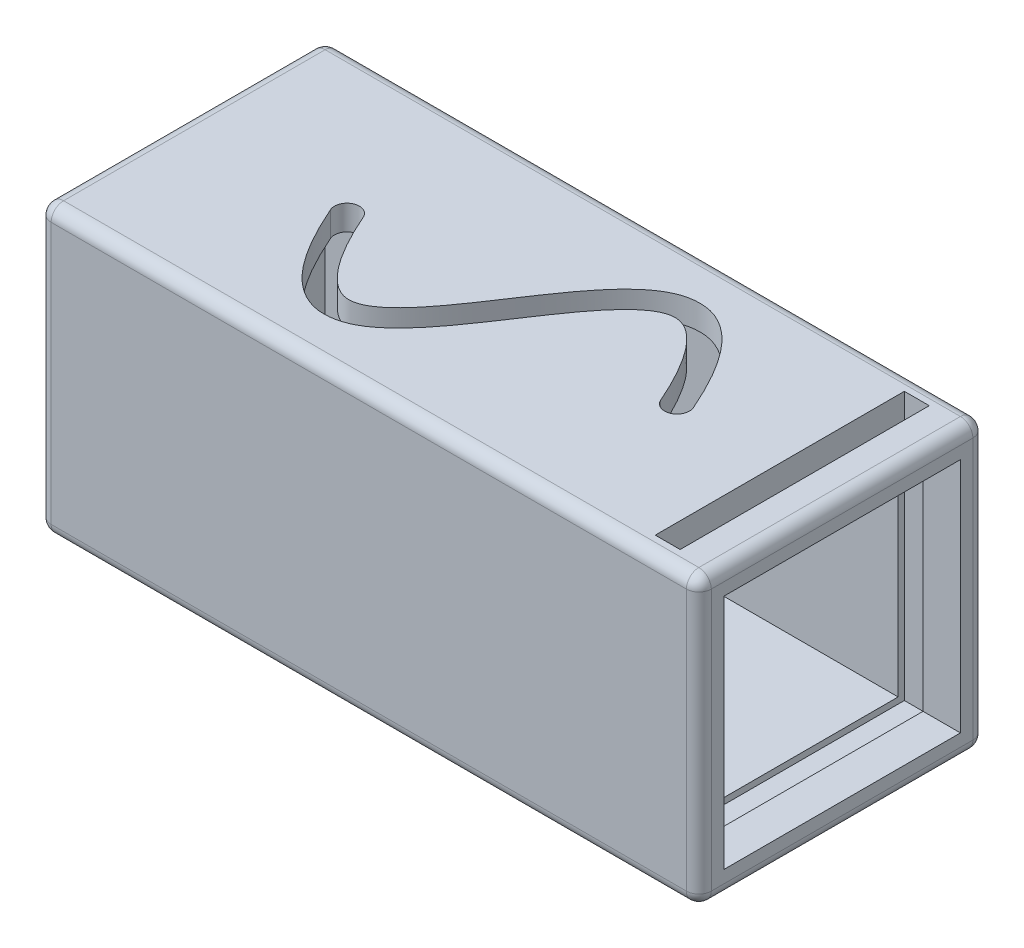
SolidWorks part; units mm, degrees
ref_plane "Front Plane" through (0, 0, 0) normal (0, 0, 1) x (1, 0, 0)
ref_plane "Top Plane" through (0, 0, 0) normal (0, 1, 0) x (1, 0, 0)
ref_plane "Right Plane" through (0, 0, 0) normal (1, 0, 0) x (0, 0, -1)
sketch "Sketch1" plane through (0, 0, 0) normal (0, 1, 0) x (1, 0, 0)
  line L0 (0, 11.5) -> (53, 11.5) construction
  line L1 (0, 0) -> (53, 0)
  line L2 (0, 0) -> (0, 23)
  line L3 (0, 23) -> (53, 23)
  line L4 (53, 0) -> (53, 23)
  line L5 (26.5, 23) -> (26.5, 0) construction
  line L6 (26.5, 23) -> (0, 0) construction
  line L7 (26.5, 23) -> (53, 0) construction
  line L8 (53, 23) -> (26.5, 0) construction
  line L9 (13.25, 11.5) -> (13.25, 23) construction
  line L10 (13.25, 11.5) -> (13.25, 0) construction
  line L11 (13.25, 23) -> (26.5, 11.5) construction
  line L12 (39.75, 11.5) -> (39.75, 0) construction
  line L13 (39.75, 0) -> (26.5, 11.5) construction
  arc A0 (14.168, 11.1034) -> (12.332, 11.8966) centre (13.25, 11.5) cw
  arc A1 (40.668, 11.1034) -> (38.832, 11.8966) centre (39.75, 11.5) ccw
  spline S0 degree 3 poles (13.25, 11.5) (17.6667, 21.7222) (26.5, 11.5) (35.3333, 1.2778) (39.75, 11.5) knots 0 0 0 0 0.5 1 1 1 1 construction
  spline S1 degree 1 poles (14.168, 11.1034) (40.668, 11.1034) knots 0 0 1 1 construction
  spline S2 degree 3 poles (14.168, 11.1034) (14.2958, 11.3992) (14.5701, 12.0052) (15.0936, 13.0483) (15.7438, 14.1469) (16.4921, 15.1239) (17.1955, 15.7936) (17.8364, 16.1939) (18.608, 16.4471) (19.553, 16.3923) (20.9516, 15.7092) (22.4917, 14.4327) (24.0966, 12.7515) (26.2868, 10.2186) (28.5265, 7.6182) (30.8893, 5.6467) (32.8016, 4.6526) (34.9868, 4.4793) (36.7555, 5.3352) (38.0231, 6.5593) (38.9304, 7.7509) (39.6641, 8.9943) (40.2372, 10.1372) (40.5305, 10.7852) (40.668, 11.1034) knots 0 0 0 0 0.015625 0.03125 0.0625 0.09375 0.125 0.15625 0.1875 0.25 0.3125 0.375 0.4375 0.5 0.625 0.6875 0.75 0.8125 0.875 0.90625 0.9375 0.96875 0.984375 1 1 1 1
  spline S3 degree 1 poles (12.332, 11.8966) (38.832, 11.8966) knots 0 0 1 1 construction
  spline S4 degree 3 poles (12.332, 11.8966) (12.4695, 12.2148) (12.7628, 12.8628) (13.3359, 14.0057) (14.0696, 15.2491) (14.9769, 16.4407) (16.2445, 17.6648) (18.0132, 18.5207) (20.1984, 18.3474) (22.1107, 17.3533) (24.4735, 15.3818) (26.7132, 12.7814) (28.9034, 10.2485) (30.5083, 8.5673) (32.0484, 7.2908) (33.447, 6.6077) (34.392, 6.5529) (35.1636, 6.8061) (35.8045, 7.2064) (36.5079, 7.8761) (37.2562, 8.8531) (37.9064, 9.9517) (38.4299, 10.9948) (38.7042, 11.6008) (38.832, 11.8966) knots 0 0 0 0 0.015625 0.03125 0.0625 0.09375 0.125 0.1875 0.25 0.3125 0.375 0.5 0.5625 0.625 0.6875 0.75 0.8125 0.84375 0.875 0.90625 0.9375 0.96875 0.984375 1 1 1 1
  dimension "D1" = 53
  dimension "D2" = 23
  dimension "D3" = 1
  dimension "D4" = 1
extrude "Boss-Extrude1" add sketch "Sketch1" along normal blind 2
sketch "Sketch3" plane through (0, 2, 0) normal (0, 1, 0) x (1, 0, 0)
  line L0 (2, 21) -> (51, 21)
  line L1 (0, 23) -> (53, 23)
  line L2 (0, 23) -> (0, 0)
  line L3 (0, 0) -> (53, 0)
  line L4 (53, 23) -> (53, 0)
  line L5 (51, 21) -> (51, 2)
  line L6 (2, 2) -> (51, 2)
  line L7 (2, 21) -> (2, 2)
  dimension "D1" = 2
extrude "Boss-Extrude2" add sketch "Sketch3" along normal blind 19
sketch "Sketch5" plane through (0, 21, 0) normal (0, 1, 0) x (1, 0, 0)
  line L1 (0, 23) -> (53, 23)
  line L2 (0, 23) -> (0, 0)
  line L3 (0, 0) -> (53, 0)
  line L4 (53, 23) -> (53, 0)
extrude "Boss-Extrude3" add sketch "Sketch5" along normal blind 2
sketch "Sketch7" plane through (0, 23, 0) normal (0, 1, 0) x (1, 0, 0)
  line L0 (0, 23) -> (26.5, 0) construction
  line L1 (0, 0) -> (53, 0) construction
  line L2 (26.5, 0) -> (53, 23) construction
  line L3 (53, 0) -> (53, 23) construction
  line L4 (53, 23) -> (0, 23) construction
  line L5 (26.5, 0) -> (26.5, 23) construction
  line L6 (13.25, 11.5) -> (39.75, 11.5) construction
  line L7 (26.5, 11.5) -> (20.8072, 4.9409) construction
  line L8 (39.75, 11.5) -> (26.5, 23) construction
  line L9 (26.5, 11.5) -> (32.1928, 18.0591) construction
  arc A0 (12.3342, 11.0983) -> (14.1658, 11.9017) centre (13.25, 11.5) cw
  arc A1 (38.8342, 11.0983) -> (40.6658, 11.9017) centre (39.75, 11.5) ccw
  spline S0 degree 3 poles (13.25, 11.5) (18.5153, -0.5021) (26.5, 11.5) (34.4847, 23.5021) (39.75, 11.5) knots 0 0 0 0 0.5 1 1 1 1 construction
  spline S1 degree 1 poles (12.3342, 11.0983) (38.8342, 11.0983) knots 0 0 1 1 construction
  spline S2 degree 3 poles (12.3342, 11.0983) (12.4963, 10.7288) (12.8406, 9.9742) (13.5006, 8.6486) (14.3249, 7.2107) (15.3106, 5.8408) (16.6448, 4.4414) (18.461, 3.4327) (20.7523, 3.6385) (22.6162, 4.8398) (24.8193, 7.1581) (26.8407, 10.2086) (28.8216, 13.1837) (30.2872, 15.1587) (31.7198, 16.6524) (32.8046, 17.2998) (33.5369, 17.4501) (34.0618, 17.4122) (34.6511, 17.1934) (35.3458, 16.7102) (36.1305, 15.8969) (36.9806, 14.7204) (37.7346, 13.4082) (38.3524, 12.1678) (38.6804, 11.4489) (38.8342, 11.0983) knots 0 0 0 0 0.015625 0.03125 0.0625 0.09375 0.125 0.1875 0.25 0.3125 0.375 0.5 0.5625 0.625 0.6875 0.75 0.78125 0.8125 0.84375 0.875 0.90625 0.9375 0.96875 0.984375 1 1 1 1
  spline S3 degree 1 poles (14.1658, 11.9017) (40.6658, 11.9017) knots 0 0 1 1 construction
  spline S4 degree 3 poles (14.1658, 11.9017) (14.3196, 11.5511) (14.6476, 10.8322) (15.2654, 9.5918) (16.0194, 8.2796) (16.8695, 7.1031) (17.6542, 6.2898) (18.3489, 5.8066) (18.9382, 5.5878) (19.4631, 5.5499) (20.1954, 5.7002) (21.2802, 6.3476) (22.7128, 7.8413) (24.1784, 9.8163) (26.1593, 12.7914) (28.1807, 15.8419) (30.3838, 18.1602) (32.2477, 19.3615) (34.539, 19.5673) (36.3552, 18.5586) (37.6894, 17.1592) (38.6751, 15.7893) (39.4994, 14.3514) (40.1594, 13.0258) (40.5037, 12.2712) (40.6658, 11.9017) knots 0 0 0 0 0.015625 0.03125 0.0625 0.09375 0.125 0.15625 0.1875 0.21875 0.25 0.3125 0.375 0.4375 0.5 0.625 0.6875 0.75 0.8125 0.875 0.90625 0.9375 0.96875 0.984375 1 1 1 1
  dimension "D1" = 1
  dimension "D2" = 1
extrude "Cut-Extrude1" cut sketch "Sketch7" against normal up to next
sketch "Sketch8" plane through (0, 0, 0) normal (-1, 0, 0) x (0, 0, 1)
  line L0 (0, 11.5) -> (-23, 11.5) construction
  line L1 (0, 23) -> (0, 0) construction
  line L2 (-23, 23) -> (-23, 0) construction
  line L3 (-4, 8) -> (-4, 15)
  line L4 (-4, 15) -> (-5.4, 15)
  line L5 (-5.4, 15) -> (-7.1, 15.5)
  line L6 (-7.1, 15.5) -> (-8.5, 15.5)
  line L7 (-8.5, 15.5) -> (-8.5, 7.5)
  line L8 (-8.5, 11.5) -> (-4, 11.5) construction
  line L9 (-4, 8) -> (-5.4, 8)
  line L10 (-5.4, 8) -> (-7.1, 7.5)
  line L11 (-7.1, 7.5) -> (-8.5, 7.5)
  dimension "D1" = 4
  dimension "D2" = 4
  dimension "D3" = 3.5
  dimension "D4" = 4.5
  dimension "D5" = 1.4
  dimension "D6" = 1.4
extrude "Cut-Extrude2" cut sketch "Sketch8" against normal up to next
sketch "Sketch9" plane through (53, 0, 0) normal (1, 0, 0) x (0, 0, -1)
  line L0 (2, 21) -> (2, 2)
  line L1 (0, 23) -> (23, 23) construction
  line L2 (0, 23) -> (0, 0) construction
  line L3 (0, 0) -> (23, 0) construction
  line L4 (23, 23) -> (23, 0) construction
  line L5 (2, 2) -> (21, 2)
  line L6 (21, 21) -> (21, 2)
  line L7 (2, 21) -> (21, 21)
  dimension "D1" = 2
extrude "Cut-Extrude3" cut sketch "Sketch9" against normal up to next
sketch "Sketch10" plane through (0, 23, 0) normal (0, 1, 0) x (1, 0, 0)
  line L0 (53, 23) -> (0, 23) construction
  line L1 (50, 21.5) -> (48, 21.5)
  line L2 (50, 21.5) -> (50, 1.5)
  line L3 (50, 1.5) -> (48, 1.5)
  line L4 (48, 21.5) -> (48, 1.5)
  line L5 (0, 0) -> (53, 0) construction
  line L6 (53, 0) -> (53, 23) construction
  dimension "D1" = 1.5
  dimension "D2" = 1.5
  dimension "D3" = 3
  dimension "D4" = 2
extrude "Cut-Extrude4" cut sketch "Sketch10" against normal blind 21.5
fillet "Fillet1" radius 1 12 edges at (53, 11.5, -23) (53, 0, -11.5) (53, 11.5, 0) (53, 23, -11.5) (0, 11.5, 0) (0, 0, -11.5) (0, 23, -11.5) (0, 11.5, -23) (26.5, 0, -23) (26.5, 0, 0) (26.5, 23, -23) (26.5, 23, 0)
